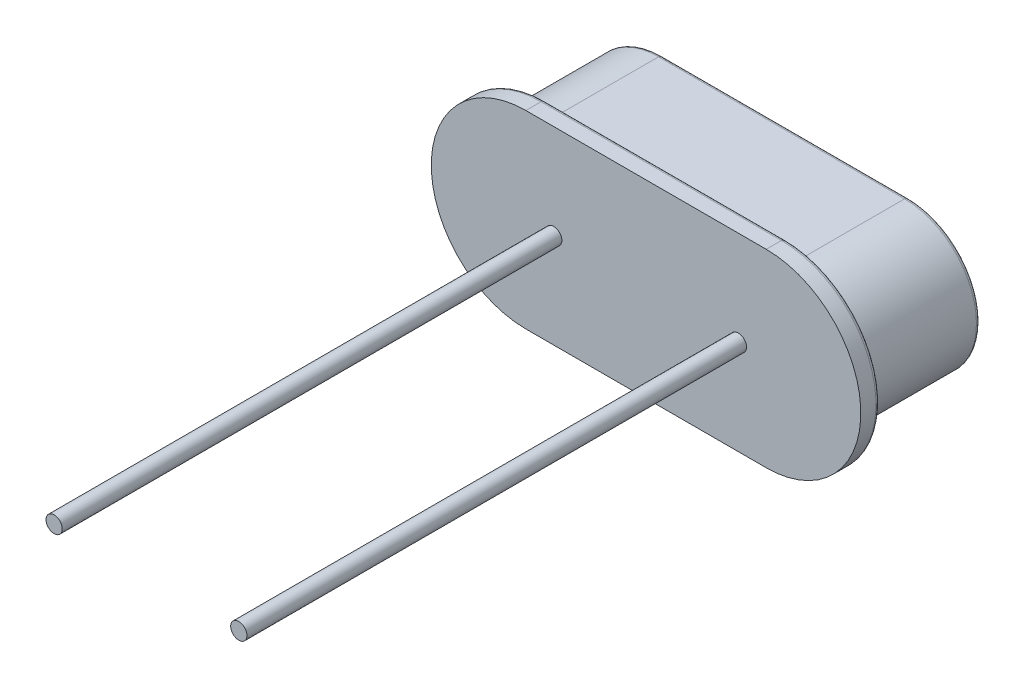
SolidWorks part; units mm, degrees
ref_plane "Front Plane" through (0, 0, 0) normal (0, 0, 1) x (1, 0, 0)
ref_plane "Top Plane" through (0, 0, 0) normal (0, 1, 0) x (1, 0, 0)
ref_plane "Right Plane" through (0, 0, 0) normal (1, 0, 0) x (0, 0, -1)
sketch "Sketch1" plane through (0, 0, 0) normal (0, 0, 1) x (1, 0, 0)
  line L0 (-3.175, 0) -> (3.175, 0) construction
  line L1 (-3.175, 2.5) -> (3.175, 2.5)
  line L2 (-3.175, -2.5) -> (3.175, -2.5)
  line L3 (-5.675, 0) -> (-5.675, 3.336) construction
  line L4 (5.675, 0) -> (5.675, 4.4657) construction
  arc A0 (-3.175, 2.5) -> (-3.175, -2.5) centre (-3.175, 0) ccw
  arc A1 (3.175, -2.5) -> (3.175, 2.5) centre (3.175, 0) ccw
  point P2 (0, 0)
  dimension "D1" = 11.35
  dimension "5" = 5
extrude "Boss-Extrude1" add sketch "Sketch1" against normal blind 0.5
sketch "Sketch3" plane through (0, 0, -0.5) normal (0, 0, -1) x (-1, 0, 0)
  line L0 (-3.25, 0) -> (3.25, 0) construction
  line L1 (-3.25, 1.9) -> (3.25, 1.9)
  line L2 (-3.25, -1.9) -> (3.25, -1.9)
  line L3 (5.15, 0) -> (5.15, -4.1369) construction
  line L4 (-5.15, 0) -> (-5.15, -4.6545) construction
  arc A0 (-3.25, 1.9) -> (-3.25, -1.9) centre (-3.25, 0) ccw
  arc A1 (3.25, -1.9) -> (3.25, 1.9) centre (3.25, 0) ccw
  point P2 (0, 0)
  dimension "D1" = 10.3
  dimension "D2" = 3.8
extrude "Boss-Extrude2" add sketch "Sketch3" along normal blind 3.18
sketch "Sketch4" plane through (0, 0, 0) normal (0, 0, 1) x (1, 0, 0)
  circle A0 centre (-2.44, 0) radius 0.215
  circle A1 centre (2.44, 0) radius 0.215
  dimension "D1" = 0.43
  dimension "0.43" = 0.43
  dimension "D2" = 4.88
  dimension "D3" = 2.44
  dimension "D4" = 2.44
extrude "Boss-Extrude3" add sketch "Sketch4" along normal blind 13.2
fillet "Fillet5" radius 0.1 4 edges at (-5.15, 0, -3.68) (0, -1.9, -3.68) (5.15, 0, -3.68) (0, 1.9, -3.68)
fillet "Fillet6" radius 0.1 4 edges at (0, -2.5, -0.5) (-5.675, 0, -0.5) (0, 2.5, -0.5) (5.675, 0, -0.5)
